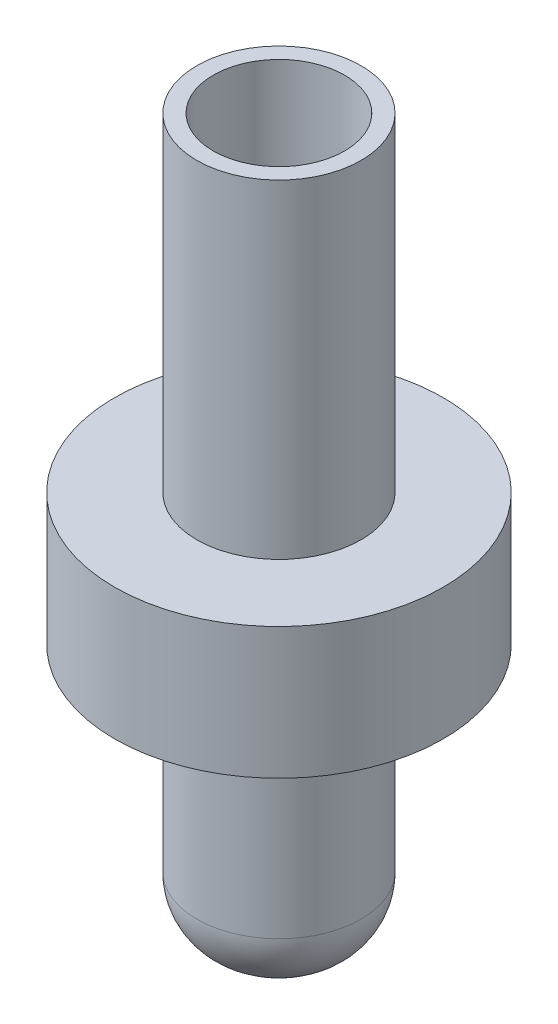
SolidWorks part; units mm, degrees
ref_plane "Front Plane" through (0, 0, 0) normal (0, 0, 1) x (1, 0, 0)
ref_plane "Top Plane" through (0, 0, 0) normal (0, 1, 0) x (1, 0, 0)
ref_plane "Right Plane" through (0, 0, 0) normal (1, 0, 0) x (0, 0, -1)
sketch "Sketch1" plane through (0, 0, 0) normal (0, 1, 0) x (1, 0, 0)
  circle A0 centre (0, 0) radius 1.25
  dimension "D1" = 2.5
extrude "Boss-Extrude1" add sketch "Sketch1" along normal blind 4
sketch "Sketch2" plane through (0, 4, 0) normal (0, 1, 0) x (1, 0, 0)
  circle A0 centre (0, 0) radius 2.5
  dimension "D1" = 5
extrude "Boss-Extrude2" add sketch "Sketch2" along normal blind 2
sketch "Sketch3" plane through (0, 6, 0) normal (0, 1, 0) x (1, 0, 0)
  circle A0 centre (0, 0) radius 1.25
  circle A1 centre (0, 0) radius 1
  dimension "D1" = 2.5
  dimension "D2" = 2
extrude "Boss-Extrude3" add sketch "Sketch3" along normal blind 5
fillet "Fillet1" radius 1 1 edges at (0, 0, 1.25)
